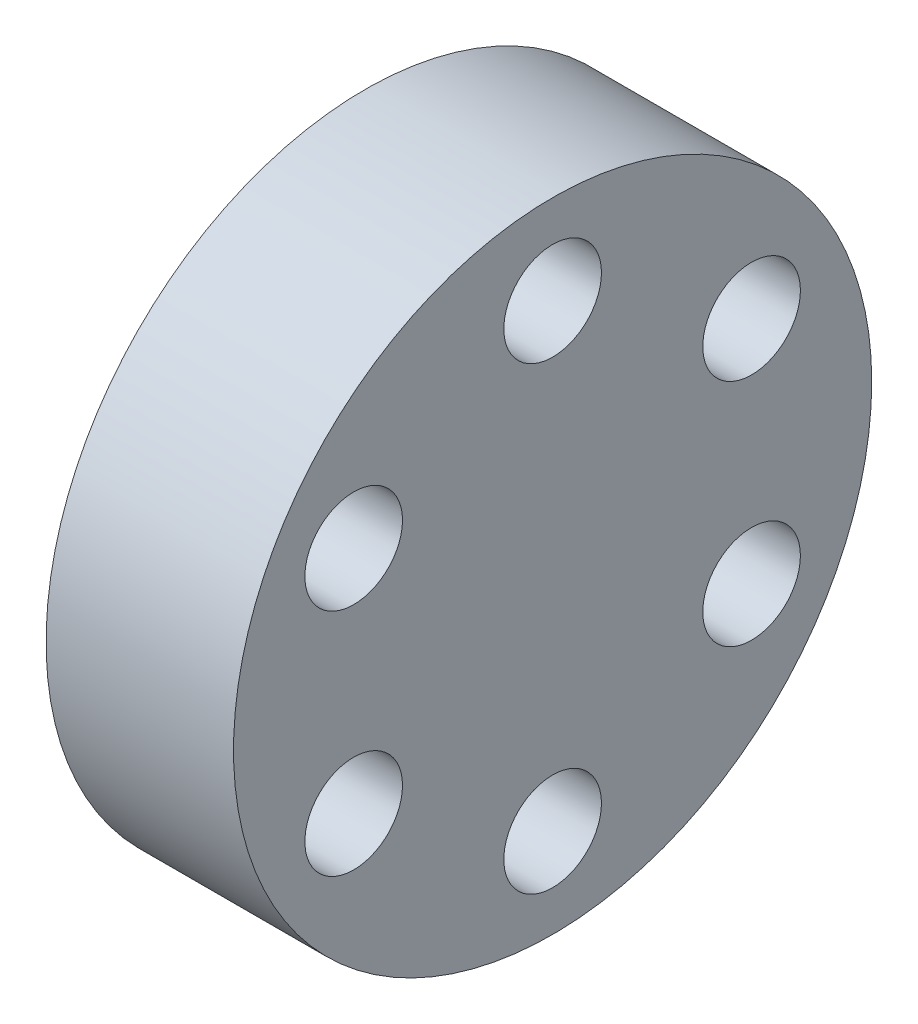
SolidWorks part; units mm, degrees
material "PET"
ref_plane "Front" through (0, 0, 0) normal (0, 0, 1) x (1, 0, 0)
ref_plane "Top" through (0, 0, 0) normal (0, 1, 0) x (1, 0, 0)
ref_plane "Right" through (0, 0, 0) normal (1, 0, 0) x (0, 0, -1)
sketch "Sketch1" plane through (0, 0, 0) normal (1, 0, 0) x (0, 0, -1)
  circle A0 centre (0, 0) radius 11.1125
  dimension "D1" = 22.225
extrude "Boss-Extrude1" add sketch "Sketch1" along normal blind 6.5278
sketch "Sketch4" plane through (6.5278, 0, 0) normal (1, 0, 0) x (0, 0, -1)
  circle A0 centre (0, 0) radius 8 construction
  point P0 (0, 8)
  point P11 (6.9282, 4)
  point P12 (6.9282, -4)
  point P13 (0, -8)
  point P14 (-6.9282, -4)
  point P15 (-6.9282, 4)
  dimension "D1" = 16
  dimension "D2" = 6
hole_wizard "M3 Clearance Hole1" positions "Sketch4" profile "Sketch3" hole size "M3" standard "ANSI Metric" end condition through all
sketch "Sketch3" plane through (6.5278, 8, 0) normal (0, 1, 0) x (0, 0, -1)
  line L0 (0, 0) -> (0, 6.5278)
  line L1 (0, 6.5278) -> (1.7, 6.5278)
  line L2 (1.7, 6.5278) -> (1.7, 0)
  line L5 (1.7, 0) -> (0, 0)
  line L11 (0, -6.35) -> (0, 107.95) construction
  dimension "Thru Hole Dia." = 3.4
  dimension "Thru Hole Depth" = 6.5278
